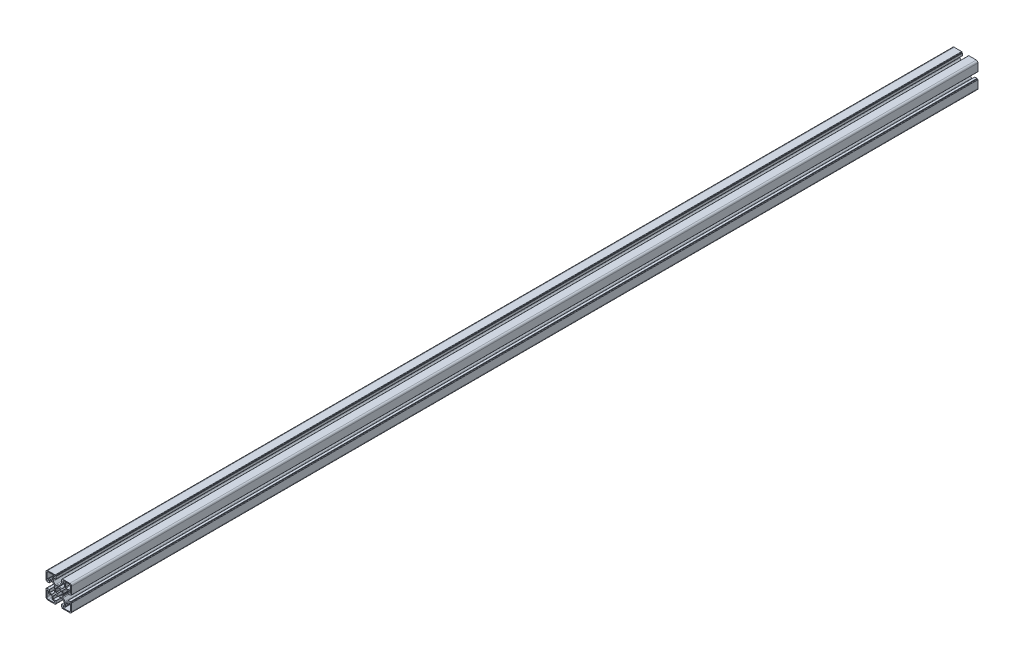
SolidWorks part; units mm, degrees
ref_plane "Front Plane" through (0, 0, 0) normal (0, 0, 1) x (1, 0, 0)
ref_plane "Top Plane" through (0, 0, 0) normal (0, 1, 0) x (1, 0, 0)
ref_plane "Right Plane" through (0, 0, 0) normal (1, 0, 0) x (0, 0, -1)
sketch "Sketch1" plane through (0, 0, 0) normal (0, 0, 1) x (1, 0, 0)
  line L0 (10.55, 18) -> (9, 18)
  line L1 (18.5, 21) -> (9, 21)
  line L2 (21, 9.0002) -> (21, 18.5)
  line L3 (18, 9.0002) -> (18, 10.55)
  line L4 (17, 11.55) -> (12.55, 11.55)
  line L5 (11.55, 12.55) -> (11.55, 17)
  line L6 (7.974, 0.7926) -> (7.5401, 0.0468)
  line L7 (-0.8674, 4.9242) -> (-0.9675, 5.4811)
  line L8 (-3.1913, 4.5626) -> (-2.864, 4.0985)
  line L9 (-4.0897, 2.8765) -> (-4.5668, 3.2082)
  line L10 (-5.4897, 0.9862) -> (-4.9205, 0.8878)
  line L11 (11.1298, 9.425) -> (7.5635, 5.8587)
  line L12 (16.3169, 9.9945) -> (12.5048, 9.9945)
  line L13 (16.5169, 5.2) -> (16.5169, 9.7945)
  line L14 (20.7196, 5) -> (16.7169, 5)
  line L15 (21.0196, 5.3) -> (21.0196, 5.5)
  line L16 (22, 5.8) -> (21.3196, 5.8)
  line L17 (22.5, 6.3) -> (22.5, 19.5)
  line L18 (19.5, 22.5) -> (6.3757, 22.5)
  line L19 (5.8757, 21.3) -> (5.8757, 22)
  line L20 (5.5757, 21) -> (5.3, 21)
  line L21 (5, 16.6668) -> (5, 20.7)
  line L22 (9.9054, 16.4668) -> (5.2, 16.4668)
  line L23 (10.1054, 12.4716) -> (10.1054, 16.2668)
  line L24 (5.9449, 7.4827) -> (9.5196, 11.0574)
  line L25 (0.1126, 7.6069) -> (0.7547, 7.9748)
  line L26 (5.4897, 0.9862) -> (4.9205, 0.8878)
  line L27 (4.0897, 2.8765) -> (4.5668, 3.2082)
  line L28 (3.1913, 4.5626) -> (2.864, 4.0985)
  line L29 (0.8674, 4.9242) -> (0.9675, 5.4811)
  line L30 (-10.55, -18) -> (-9, -18)
  line L31 (-18.5, -21) -> (-9, -21)
  line L32 (-21, -9.0002) -> (-21, -18.5)
  line L33 (-18, -9.0002) -> (-18, -10.55)
  line L34 (-17, -11.55) -> (-12.55, -11.55)
  line L35 (-11.55, -12.55) -> (-11.55, -17)
  line L36 (-7.974, -0.7926) -> (-7.5401, -0.0468)
  line L37 (-11.1298, -9.425) -> (-7.5635, -5.8587)
  line L38 (-16.3169, -9.9945) -> (-12.5048, -9.9945)
  line L39 (-16.5169, -5.2) -> (-16.5169, -9.7945)
  line L40 (-20.7196, -5) -> (-16.7169, -5)
  line L41 (-21.0196, -5.3) -> (-21.0196, -5.5)
  line L42 (-22, -5.8) -> (-21.3196, -5.8)
  line L43 (-22.5, -6.3) -> (-22.5, -19.5)
  line L44 (-19.5, -22.5) -> (-6.3757, -22.5)
  line L45 (-5.8757, -21.3) -> (-5.8757, -22)
  line L46 (-5.5757, -21) -> (-5.3, -21)
  line L47 (-5, -16.6668) -> (-5, -20.7)
  line L48 (-9.9054, -16.4668) -> (-5.2, -16.4668)
  line L49 (-10.1054, -12.4716) -> (-10.1054, -16.2668)
  line L50 (-5.9449, -7.4827) -> (-9.5196, -11.0574)
  line L51 (-0.1126, -7.6069) -> (-0.7547, -7.9748)
  line L52 (0.8674, -4.9242) -> (0.9675, -5.4811)
  line L53 (3.1913, -4.5626) -> (2.864, -4.0985)
  line L54 (4.0897, -2.8765) -> (4.5668, -3.2082)
  line L55 (5.4897, -0.9862) -> (4.9205, -0.8878)
  line L56 (0.1126, -7.6069) -> (0.7547, -7.9748)
  line L57 (5.9449, -7.4827) -> (9.5196, -11.0574)
  line L58 (10.1054, -12.4716) -> (10.1054, -16.2668)
  line L59 (9.9054, -16.4668) -> (5.2, -16.4668)
  line L60 (5, -16.6668) -> (5, -20.7)
  line L61 (5.5757, -21) -> (5.3, -21)
  line L62 (-0.1126, 7.6069) -> (-0.7547, 7.9748)
  line L63 (-5.9449, 7.4827) -> (-9.5196, 11.0574)
  line L64 (-10.1054, 12.4716) -> (-10.1054, 16.2668)
  line L65 (-9.9054, 16.4668) -> (-5.2, 16.4668)
  line L66 (-5, 16.6668) -> (-5, 20.7)
  line L67 (-5.5757, 21) -> (-5.3, 21)
  line L68 (-5.8757, 21.3) -> (-5.8757, 22)
  line L69 (-19.5, 22.5) -> (-6.3757, 22.5)
  line L70 (-22.5, 6.3) -> (-22.5, 19.5)
  line L71 (-22, 5.8) -> (-21.3196, 5.8)
  line L72 (-21.0196, 5.3) -> (-21.0196, 5.5)
  line L73 (-20.7196, 5) -> (-16.7169, 5)
  line L74 (-16.5169, 5.2) -> (-16.5169, 9.7945)
  line L75 (-16.3169, 9.9945) -> (-12.5048, 9.9945)
  line L76 (-11.1298, 9.425) -> (-7.5635, 5.8587)
  line L77 (-7.974, 0.7926) -> (-7.5401, 0.0468)
  line L78 (5.8757, -21.3) -> (5.8757, -22)
  line L79 (19.5, -22.5) -> (6.3757, -22.5)
  line L80 (22.5, -6.3) -> (22.5, -19.5)
  line L81 (22, -5.8) -> (21.3196, -5.8)
  line L82 (21.0196, -5.3) -> (21.0196, -5.5)
  line L83 (20.7196, -5) -> (16.7169, -5)
  line L84 (16.5169, -5.2) -> (16.5169, -9.7945)
  line L85 (16.3169, -9.9945) -> (12.5048, -9.9945)
  line L86 (11.1298, -9.425) -> (7.5635, -5.8587)
  line L87 (-5.4897, -0.9862) -> (-4.9205, -0.8878)
  line L88 (-4.0897, -2.8765) -> (-4.5668, -3.2082)
  line L89 (-3.1913, -4.5626) -> (-2.864, -4.0985)
  line L90 (-0.8674, -4.9242) -> (-0.9675, -5.4811)
  line L91 (7.974, -0.7926) -> (7.5401, -0.0468)
  line L92 (-11.55, 12.55) -> (-11.55, 17)
  line L93 (-17, 11.55) -> (-12.55, 11.55)
  line L94 (-18, 9.0002) -> (-18, 10.55)
  line L95 (-21, 9.0002) -> (-21, 18.5)
  line L96 (-18.5, 21) -> (-9, 21)
  line L97 (-10.55, 18) -> (-9, 18)
  line L98 (11.55, -12.55) -> (11.55, -17)
  line L99 (17, -11.55) -> (12.55, -11.55)
  line L100 (18, -9.0002) -> (18, -10.55)
  line L101 (21, -9.0002) -> (21, -18.5)
  line L102 (18.5, -21) -> (9, -21)
  line L103 (10.55, -18) -> (9, -18)
  line L104 (-33.3633, 0) -> (37.7265, 0) construction
  line L105 (0, 32.2957) -> (0, -36.0465) construction
  arc A0 (9, 18) -> (9, 21) centre (9, 19.5) cw
  arc A1 (18.5, 21) -> (21, 18.5) centre (18.5, 18.5) cw
  arc A2 (21, 9.0002) -> (18, 9.0002) centre (19.5, 9.0002) cw
  arc A3 (17, 11.55) -> (18, 10.55) centre (17, 10.55) cw
  arc A4 (12.55, 11.55) -> (11.55, 12.55) centre (12.55, 12.55) cw
  arc A5 (10.55, 18) -> (11.55, 17) centre (10.55, 17) cw
  arc A6 (7.5313, 0) -> (7.5401, 0.0468) centre (7.7309, -0.013) cw
  arc A7 (8, 0.9141) -> (7.974, 0.7926) centre (7.8011, 0.8932) cw
  arc A8 (7.2004, 3.6119) -> (8, 0.9141) centre (0.0496, 0.0249) cw
  arc A9 (7.2004, 3.6119) -> (7.5635, 5.8587) centre (8.9385, 4.4837) cw
  arc A10 (11.1298, 9.425) -> (12.5048, 9.9945) centre (12.5048, 8.05) cw
  arc A11 (16.3169, 9.9945) -> (16.5169, 9.7945) centre (16.3169, 9.7945) cw
  arc A12 (16.7169, 5) -> (16.5169, 5.2) centre (16.7169, 5.2) cw
  arc A13 (21.0196, 5.3) -> (20.7196, 5) centre (20.7196, 5.3) cw
  arc A14 (0.8674, 4.9242) -> (-0.8674, 4.9242) centre (0, 0) ccw
  arc A15 (-0.9675, 5.4811) -> (-1.5951, 5.8941) centre (-1.4627, 5.4119) ccw
  arc A16 (-1.5951, 5.8941) -> (-3.0444, 5.2994) centre (-0.0235, 0) ccw
  arc A17 (-3.0444, 5.2994) -> (-3.1913, 4.5626) centre (-2.7943, 4.8665) ccw
  arc A18 (-2.864, 4.0985) -> (-4.0897, 2.8765) centre (0, 0) ccw
  arc A19 (-4.5668, 3.2082) -> (-5.3025, 3.0565) centre (-4.868, 2.8091) ccw
  arc A20 (-5.3025, 3.0565) -> (-5.9068, 1.6112) centre (-0.0235, 0) ccw
  arc A21 (-5.9068, 1.6112) -> (-5.4897, 0.9862) centre (-5.4239, 1.4819) ccw
  arc A22 (-4.9205, 0.8878) -> (-5, 0) centre (0, 0) ccw
  arc A23 (21.0196, 5.5) -> (21.3196, 5.8) centre (21.3196, 5.5) cw
  arc A24 (22.5, 6.3) -> (22, 5.8) centre (22, 6.3) cw
  arc A25 (19.5, 22.5) -> (22.5, 19.5) centre (19.5, 19.5) cw
  arc A26 (5.8757, 22) -> (6.3757, 22.5) centre (6.3757, 22) cw
  arc A27 (5.8757, 21.3) -> (5.5757, 21) centre (5.5757, 21.3) cw
  arc A28 (5, 20.7) -> (5.3, 21) centre (5.3, 20.7) cw
  arc A29 (5.2, 16.4668) -> (5, 16.6668) centre (5.2, 16.6668) cw
  arc A30 (9.9054, 16.4668) -> (10.1054, 16.2668) centre (9.9054, 16.2668) cw
  arc A31 (10.1054, 12.4716) -> (9.5196, 11.0574) centre (8.1054, 12.4716) cw
  arc A32 (5.9449, 7.4827) -> (3.6665, 7.1733) centre (4.5855, 8.9496) cw
  arc A33 (0.8764, 8) -> (3.6665, 7.1733) centre (0.0235, 0) cw
  arc A34 (0.7547, 7.9748) -> (0.8764, 8) centre (0.8542, 7.8013) cw
  arc A35 (0.1126, 7.6069) -> (0, 7.531) centre (-0.0489, 7.7249) cw
  arc A36 (4.9205, 0.8878) -> (5, 0) centre (0, 0) cw
  arc A37 (5.9068, 1.6112) -> (5.4897, 0.9862) centre (5.4239, 1.4819) cw
  arc A38 (5.3025, 3.0565) -> (5.9068, 1.6112) centre (0.0235, 0) cw
  arc A39 (4.5668, 3.2082) -> (5.3025, 3.0565) centre (4.868, 2.8091) cw
  arc A40 (2.864, 4.0985) -> (4.0897, 2.8765) centre (0, 0) cw
  arc A41 (3.0444, 5.2994) -> (3.1913, 4.5626) centre (2.7943, 4.8665) cw
  arc A42 (1.5951, 5.8941) -> (3.0444, 5.2994) centre (0.0235, 0) cw
  arc A43 (0.9675, 5.4811) -> (1.5951, 5.8941) centre (1.4627, 5.4119) cw
  arc A44 (-9, -18) -> (-9, -21) centre (-9, -19.5) cw
  arc A45 (-18.5, -21) -> (-21, -18.5) centre (-18.5, -18.5) cw
  arc A46 (-21, -9.0002) -> (-18, -9.0002) centre (-19.5, -9.0002) cw
  arc A47 (-17, -11.55) -> (-18, -10.55) centre (-17, -10.55) cw
  arc A48 (-12.55, -11.55) -> (-11.55, -12.55) centre (-12.55, -12.55) cw
  arc A49 (-10.55, -18) -> (-11.55, -17) centre (-10.55, -17) cw
  arc A50 (-7.5313, 0) -> (-7.5401, -0.0468) centre (-7.7309, 0.013) cw
  arc A51 (-8, -0.9141) -> (-7.974, -0.7926) centre (-7.8011, -0.8932) cw
  arc A52 (-7.2004, -3.6119) -> (-8, -0.9141) centre (-0.0496, -0.0249) cw
  arc A53 (-7.2004, -3.6119) -> (-7.5635, -5.8587) centre (-8.9385, -4.4837) cw
  arc A54 (-11.1298, -9.425) -> (-12.5048, -9.9945) centre (-12.5048, -8.05) cw
  arc A55 (-16.3169, -9.9945) -> (-16.5169, -9.7945) centre (-16.3169, -9.7945) cw
  arc A56 (-16.7169, -5) -> (-16.5169, -5.2) centre (-16.7169, -5.2) cw
  arc A57 (-21.0196, -5.3) -> (-20.7196, -5) centre (-20.7196, -5.3) cw
  arc A58 (-21.0196, -5.5) -> (-21.3196, -5.8) centre (-21.3196, -5.5) cw
  arc A59 (-22.5, -6.3) -> (-22, -5.8) centre (-22, -6.3) cw
  arc A60 (-19.5, -22.5) -> (-22.5, -19.5) centre (-19.5, -19.5) cw
  arc A61 (-5.8757, -22) -> (-6.3757, -22.5) centre (-6.3757, -22) cw
  arc A62 (-5.8757, -21.3) -> (-5.5757, -21) centre (-5.5757, -21.3) cw
  arc A63 (-5, -20.7) -> (-5.3, -21) centre (-5.3, -20.7) cw
  arc A64 (-5.2, -16.4668) -> (-5, -16.6668) centre (-5.2, -16.6668) cw
  arc A65 (-9.9054, -16.4668) -> (-10.1054, -16.2668) centre (-9.9054, -16.2668) cw
  arc A66 (-10.1054, -12.4716) -> (-9.5196, -11.0574) centre (-8.1054, -12.4716) cw
  arc A67 (-5.9449, -7.4827) -> (-3.6665, -7.1733) centre (-4.5855, -8.9496) cw
  arc A68 (-0.8764, -8) -> (-3.6665, -7.1733) centre (-0.0235, 0) cw
  arc A69 (-0.7547, -7.9748) -> (-0.8764, -8) centre (-0.8542, -7.8013) cw
  arc A70 (-0.1126, -7.6069) -> (0, -7.531) centre (0.0489, -7.7249) cw
  arc A71 (0.9675, -5.4811) -> (1.5951, -5.8941) centre (1.4627, -5.4119) ccw
  arc A72 (1.5951, -5.8941) -> (3.0444, -5.2994) centre (0.0235, 0) ccw
  arc A73 (3.0444, -5.2994) -> (3.1913, -4.5626) centre (2.7943, -4.8665) ccw
  arc A74 (2.864, -4.0985) -> (4.0897, -2.8765) centre (0, 0) ccw
  arc A75 (4.5668, -3.2082) -> (5.3025, -3.0565) centre (4.868, -2.8091) ccw
  arc A76 (5.3025, -3.0565) -> (5.9068, -1.6112) centre (0.0235, 0) ccw
  arc A77 (5.9068, -1.6112) -> (5.4897, -0.9862) centre (5.4239, -1.4819) ccw
  arc A78 (4.9205, -0.8878) -> (5, 0) centre (0, 0) ccw
  arc A79 (0.1126, -7.6069) -> (0, -7.531) centre (-0.0489, -7.7249) ccw
  arc A80 (0.7547, -7.9748) -> (0.8764, -8) centre (0.8542, -7.8013) ccw
  arc A81 (0.8764, -8) -> (3.6665, -7.1733) centre (0.0235, 0) ccw
  arc A82 (5.9449, -7.4827) -> (3.6665, -7.1733) centre (4.5855, -8.9496) ccw
  arc A83 (10.1054, -12.4716) -> (9.5196, -11.0574) centre (8.1054, -12.4716) ccw
  arc A84 (9.9054, -16.4668) -> (10.1054, -16.2668) centre (9.9054, -16.2668) ccw
  arc A85 (5.2, -16.4668) -> (5, -16.6668) centre (5.2, -16.6668) ccw
  arc A86 (5, -20.7) -> (5.3, -21) centre (5.3, -20.7) ccw
  arc A87 (5.8757, -21.3) -> (5.5757, -21) centre (5.5757, -21.3) ccw
  arc A88 (-0.1126, 7.6069) -> (0, 7.531) centre (0.0489, 7.7249) ccw
  arc A89 (-0.7547, 7.9748) -> (-0.8764, 8) centre (-0.8542, 7.8013) ccw
  arc A90 (-0.8764, 8) -> (-3.6665, 7.1733) centre (-0.0235, 0) ccw
  arc A91 (-5.9449, 7.4827) -> (-3.6665, 7.1733) centre (-4.5855, 8.9496) ccw
  arc A92 (-10.1054, 12.4716) -> (-9.5196, 11.0574) centre (-8.1054, 12.4716) ccw
  arc A93 (-9.9054, 16.4668) -> (-10.1054, 16.2668) centre (-9.9054, 16.2668) ccw
  arc A94 (-5.2, 16.4668) -> (-5, 16.6668) centre (-5.2, 16.6668) ccw
  arc A95 (-5, 20.7) -> (-5.3, 21) centre (-5.3, 20.7) ccw
  arc A96 (-5.8757, 21.3) -> (-5.5757, 21) centre (-5.5757, 21.3) ccw
  arc A97 (-5.8757, 22) -> (-6.3757, 22.5) centre (-6.3757, 22) ccw
  arc A98 (-19.5, 22.5) -> (-22.5, 19.5) centre (-19.5, 19.5) ccw
  arc A99 (-22.5, 6.3) -> (-22, 5.8) centre (-22, 6.3) ccw
  arc A100 (-21.0196, 5.5) -> (-21.3196, 5.8) centre (-21.3196, 5.5) ccw
  arc A101 (-21.0196, 5.3) -> (-20.7196, 5) centre (-20.7196, 5.3) ccw
  arc A102 (-16.7169, 5) -> (-16.5169, 5.2) centre (-16.7169, 5.2) ccw
  arc A103 (-16.3169, 9.9945) -> (-16.5169, 9.7945) centre (-16.3169, 9.7945) ccw
  arc A104 (-11.1298, 9.425) -> (-12.5048, 9.9945) centre (-12.5048, 8.05) ccw
  arc A105 (-7.2004, 3.6119) -> (-7.5635, 5.8587) centre (-8.9385, 4.4837) ccw
  arc A106 (-7.2004, 3.6119) -> (-8, 0.9141) centre (-0.0496, 0.0249) ccw
  arc A107 (-8, 0.9141) -> (-7.974, 0.7926) centre (-7.8011, 0.8932) ccw
  arc A108 (-7.5313, 0) -> (-7.5401, 0.0468) centre (-7.7309, -0.013) ccw
  arc A109 (5.8757, -22) -> (6.3757, -22.5) centre (6.3757, -22) ccw
  arc A110 (19.5, -22.5) -> (22.5, -19.5) centre (19.5, -19.5) ccw
  arc A111 (22.5, -6.3) -> (22, -5.8) centre (22, -6.3) ccw
  arc A112 (21.0196, -5.5) -> (21.3196, -5.8) centre (21.3196, -5.5) ccw
  arc A113 (-4.9205, -0.8878) -> (-5, 0) centre (0, 0) cw
  arc A114 (-5.9068, -1.6112) -> (-5.4897, -0.9862) centre (-5.4239, -1.4819) cw
  arc A115 (-5.3025, -3.0565) -> (-5.9068, -1.6112) centre (-0.0235, 0) cw
  arc A116 (-4.5668, -3.2082) -> (-5.3025, -3.0565) centre (-4.868, -2.8091) cw
  arc A117 (-2.864, -4.0985) -> (-4.0897, -2.8765) centre (0, 0) cw
  arc A118 (-3.0444, -5.2994) -> (-3.1913, -4.5626) centre (-2.7943, -4.8665) cw
  arc A119 (-1.5951, -5.8941) -> (-3.0444, -5.2994) centre (-0.0235, 0) cw
  arc A120 (-0.9675, -5.4811) -> (-1.5951, -5.8941) centre (-1.4627, -5.4119) cw
  arc A121 (0.8674, -4.9242) -> (-0.8674, -4.9242) centre (0, 0) cw
  arc A122 (21.0196, -5.3) -> (20.7196, -5) centre (20.7196, -5.3) ccw
  arc A123 (16.7169, -5) -> (16.5169, -5.2) centre (16.7169, -5.2) ccw
  arc A124 (-10.55, 18) -> (-11.55, 17) centre (-10.55, 17) ccw
  arc A125 (-12.55, 11.55) -> (-11.55, 12.55) centre (-12.55, 12.55) ccw
  arc A126 (-17, 11.55) -> (-18, 10.55) centre (-17, 10.55) ccw
  arc A127 (-21, 9.0002) -> (-18, 9.0002) centre (-19.5, 9.0002) ccw
  arc A128 (-18.5, 21) -> (-21, 18.5) centre (-18.5, 18.5) ccw
  arc A129 (-9, 18) -> (-9, 21) centre (-9, 19.5) ccw
  arc A130 (16.3169, -9.9945) -> (16.5169, -9.7945) centre (16.3169, -9.7945) ccw
  arc A131 (11.1298, -9.425) -> (12.5048, -9.9945) centre (12.5048, -8.05) ccw
  arc A132 (7.2004, -3.6119) -> (7.5635, -5.8587) centre (8.9385, -4.4837) ccw
  arc A133 (7.2004, -3.6119) -> (8, -0.9141) centre (0.0496, -0.0249) ccw
  arc A134 (8, -0.9141) -> (7.974, -0.7926) centre (7.8011, -0.8932) ccw
  arc A135 (7.5313, 0) -> (7.5401, -0.0468) centre (7.7309, 0.013) ccw
  arc A136 (10.55, -18) -> (11.55, -17) centre (10.55, -17) ccw
  arc A137 (12.55, -11.55) -> (11.55, -12.55) centre (12.55, -12.55) ccw
  arc A138 (17, -11.55) -> (18, -10.55) centre (17, -10.55) ccw
  arc A139 (21, -9.0002) -> (18, -9.0002) centre (19.5, -9.0002) ccw
  arc A140 (18.5, -21) -> (21, -18.5) centre (18.5, -18.5) ccw
  arc A141 (9, -18) -> (9, -21) centre (9, -19.5) ccw
  dimension "D6" = 12.2
  dimension "D8" = 10
  dimension "D1" = 10
  dimension "D2" = 45
  dimension "D3" = 45
  dimension "D4" = 10
  dimension "D5" = 14.5
  dimension "D7" = 22.5
extrude "Base-Extrude" add sketch "Sketch1" against normal blind 1600
hole_wizard "M12 Hole Left" positions "Sketch11" profile "Sketch10" tap size "M12x1.25" standard "ISO"
sketch "Sketch11" plane through (0, 0, 0) normal (0, 0, 1) x (1, 0, 0)
  point P0 (0, 0)
cosmetic thread "Hole Thread5" parameters "D1"=55, "D2"=12
sketch "Sketch10" plane through (0, 0, 0) normal (1, 0, 0) x (0, -1, 0)
  line L0 (0, 0) -> (0, 58.2446)
  line L1 (0, 58.2446) -> (5.4, 55)
  line L2 (5.4, 55) -> (5.4, 0)
  line L5 (5.4, 0) -> (0, 0)
  line L10 (0, 58.2446) -> (-5.4, 55) construction
  line L11 (0, -6.35) -> (0, 107.95) construction
  dimension "Tap Drill Dia." = 10.8
  dimension "Tap Drill Depth" = 55
  dimension "Drill Angle" = 118
